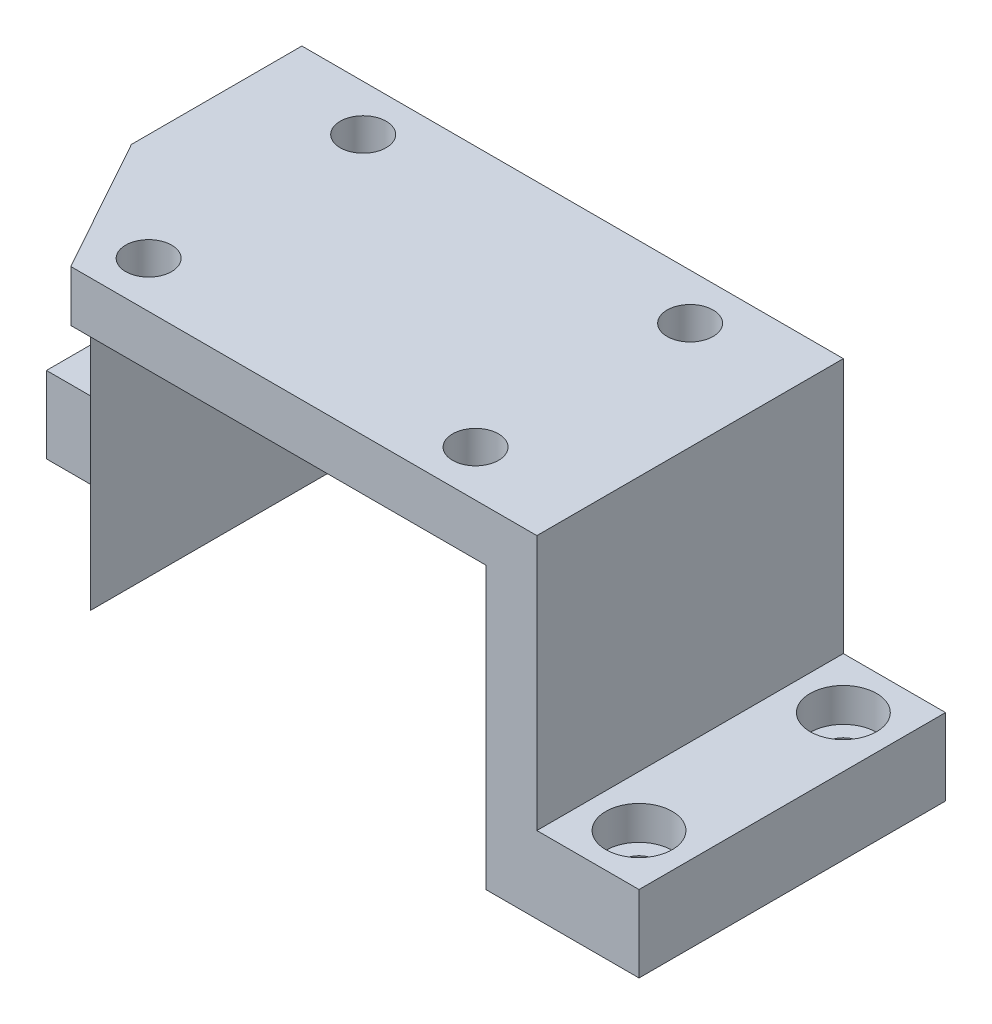
SolidWorks part; units mm, degrees
material "1.0045 (S355JR)"
ref_plane "Front Plane" through (0, 0, 0) normal (0, 0, 1) x (1, 0, 0)
ref_plane "Top Plane" through (0, 0, 0) normal (0, 1, 0) x (1, 0, 0)
ref_plane "Right Plane" through (0, 0, 0) normal (1, 0, 0) x (0, 0, -1)
sketch "Sketch1" plane through (0, 0, 0) normal (0, 1, 0) x (1, 0, 0)
  line L1 (-53, -30) -> (53, -30)
  line L2 (-53, -30) -> (-53, 30)
  line L3 (-53, 30) -> (53, 30)
  line L4 (53, -30) -> (53, 30)
  line L5 (-53, -30) -> (53, 30) construction
  line L6 (-53, 30) -> (53, -30) construction
  point P0 (0, 0)
  dimension "D1" = 60
  dimension "D2" = 106
extrude "Boss-Extrude1" add sketch "Sketch1" along normal blind 10
sketch "Sketch2" plane through (0, 0, 0) normal (0, -1, 0) x (1, 0, 0)
  line L0 (53, -30) -> (-53, -30) construction
  line L1 (-53, 30) -> (-43, 30)
  line L2 (-53, 30) -> (-53, -30)
  line L3 (-53, -30) -> (-43, -30)
  line L4 (-43, 30) -> (-43, -30)
  line L6 (53, 30) -> (43, 30)
  line L7 (53, 30) -> (53, -30)
  line L8 (53, -30) -> (43, -30)
  line L9 (43, 30) -> (43, -30)
  dimension "D1" = 10
  dimension "D2" = 10
extrude "Boss-Extrude2" add sketch "Sketch2" along normal blind 55
sketch "Sketch3" plane through (53, 0, 0) normal (1, 0, 0) x (0, 0, -1)
  line L0 (30, 10) -> (30, -55) construction
  line L1 (-30, -55) -> (30, -55)
  line L2 (-30, -55) -> (-30, -40)
  line L3 (-30, -40) -> (30, -40)
  line L4 (30, -55) -> (30, -40)
  dimension "D1" = 15
extrude "Boss-Extrude3" add sketch "Sketch3" along normal blind 20
sketch "Sketch4" plane through (-53, 0, 0) normal (-1, 0, 0) x (0, 0, 1)
  line L1 (-30, -55) -> (0, -55)
  line L2 (-30, -55) -> (-30, -40)
  line L3 (-30, -40) -> (0, -40)
  line L5 (0, -40) -> (0, -55)
  dimension "D1" = 15
  dimension "D2" = 30
extrude "Boss-Extrude4" add sketch "Sketch4" along normal blind 20
sketch "Sketch5" plane through (0, 10, 0) normal (0, 1, 0) x (1, 0, 0)
  line L0 (0, 0) -> (0, 30) construction
  line L1 (53, 30) -> (-53, 30) construction
  line L2 (0, 0) -> (18.8591, 0) construction
  circle A0 centre (-32, 21) radius 4.5
  circle A1 centre (32, 21) radius 4.5
  circle A2 centre (32, -21) radius 4.5
  circle A3 centre (-32, -21) radius 4.5
  dimension "D3" = 9
  dimension "D1" = 32
  dimension "D2" = 21
extrude "Cut-Extrude1" cut sketch "Sketch5" against normal through all
sketch "Sketch6" plane through (0, -40, 0) normal (0, 1, 0) x (1, 0, 0)
  line L0 (73, 30) -> (53, 30) construction
  line L1 (73, 30) -> (73, -30) construction
  line L2 (73, -30) -> (53, -30) construction
  line L3 (-73, 0) -> (-73, 30) construction
  line L4 (-73, 30) -> (-53, 30) construction
  circle A0 centre (63, 20) radius 6.5
  circle A1 centre (63, -20) radius 6.5
  circle A2 centre (-63, 20) radius 6.5
  dimension "D2" = 10
  dimension "D10" = 13
  dimension "D11" = 13
  dimension "D12" = 13
  dimension "D1" = 10
  dimension "D3" = 10
  dimension "D4" = 10
  dimension "D5" = 10
  dimension "D6" = 10
extrude "Cut-Extrude2" cut sketch "Sketch6" against normal blind 6.6
sketch "Sketch7" plane through (0, -46.6, 0) normal (0, 1, 0) x (1, 0, 0)
  circle A0 centre (-63, 20) radius 3.3
  circle A2 centre (63, -20) radius 3.3
  circle A3 centre (63, 20) radius 3.3
  dimension "D1" = 6.6
  dimension "D3" = 6.6
  dimension "D4" = 6.6
extrude "Cut-Extrude3" cut sketch "Sketch7" against normal through all
sketch "Sketch8" plane through (0, 10, 0) normal (0, 1, 0) x (1, 0, 0)
  line L0 (-53, -30) -> (53, -30) construction
  line L1 (53, 30) -> (53, -30) construction
  line L2 (-38.239, -30) -> (-53, -3.3705)
  line L3 (-53, 30) -> (-53, -30) construction
  line L4 (-53, -3.3705) -> (-53, -30)
  line L5 (-53, -30) -> (-38.239, -30)
  point P0 (-38.239, -30)
  dimension "D1" = 91.239
  dimension "D2" = 119
extrude "Cut-Extrude4" cut sketch "Sketch8" against normal through all
